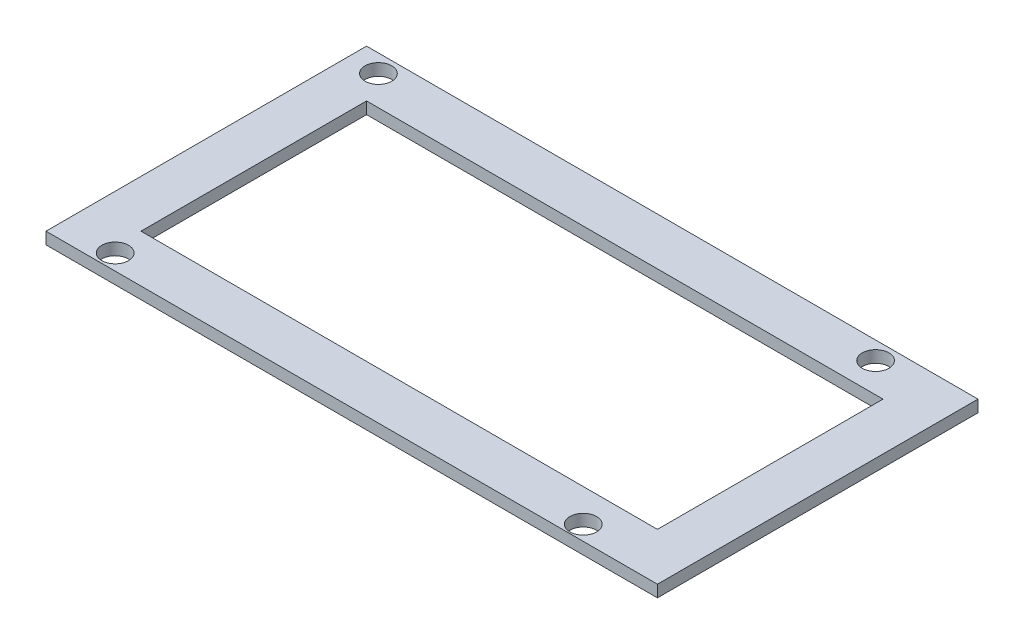
SolidWorks part; units mm, degrees
ref_plane "Front Plane" through (0, 0, 0) normal (0, 0, 1) x (1, 0, 0)
ref_plane "Top Plane" through (0, 0, 0) normal (0, 1, 0) x (1, 0, 0)
ref_plane "Right Plane" through (0, 0, 0) normal (1, 0, 0) x (0, 0, -1)
sketch "Sketch1" plane through (0, 0, 0) normal (0, 1, 0) x (1, 0, 0)
  line L11 (0, 54) -> (103, 54)
  line L12 (0, 54) -> (0, 0)
  line L13 (0, 0) -> (103, 0)
  line L14 (103, 54) -> (103, 0)
  line L15 (8, 46) -> (8, 8)
  line L16 (8, 8) -> (95, 8)
  line L17 (95, 46) -> (95, 8)
  line L18 (8, 46) -> (95, 46)
  circle A0 centre (88.75, 51) radius 2.25
  circle A1 centre (88, 2.5) radius 2.25
  circle A2 centre (5, 51) radius 2.25
  circle A3 centre (9, 2.65) radius 2.25
  dimension "D11" = 4.5
  dimension "D1" = 103
  dimension "D2" = 54
  dimension "D3" = 8
  dimension "D4" = 8
  dimension "D5" = 3
  dimension "D6" = 14.25
  dimension "D7" = 15
  dimension "D8" = 2.5
  dimension "D9" = 3
  dimension "D10" = 5
  dimension "D12" = 2.65
  dimension "D13" = 9
  dimension "D14" = 8
  dimension "D15" = 8
  dimension "D16" = 0
  dimension "D17" = 0
extrude "Boss-Extrude1" add sketch "Sketch1" along normal blind 2
